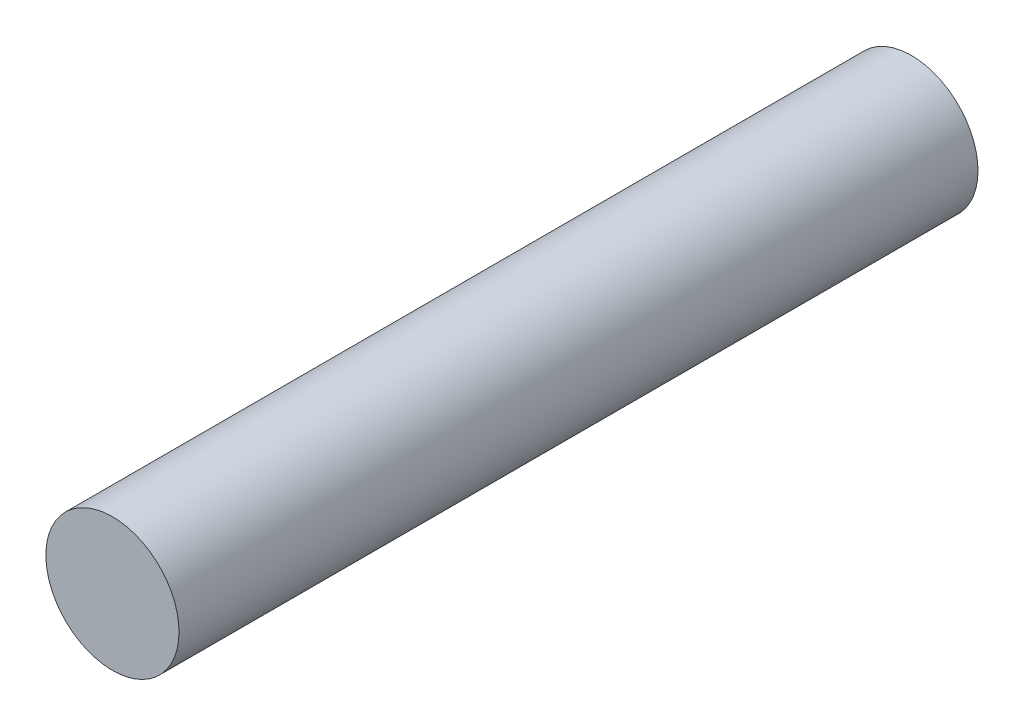
SolidWorks part; units mm, degrees
ref_plane "Front Plane" through (0, 0, 0) normal (0, 0, 1) x (1, 0, 0)
ref_plane "Top Plane" through (0, 0, 0) normal (0, 1, 0) x (1, 0, 0)
ref_plane "Right Plane" through (0, 0, 0) normal (1, 0, 0) x (0, 0, -1)
sketch "Sketch1" plane through (0, 0, 15) normal (0, 0, 1) x (1, 0, 0)
  circle A0 centre (-19, 30.4286) radius 2.5
  dimension "D1" = 5
extrude "Boss-Extrude1" add sketch "Sketch1" against normal blind 30
